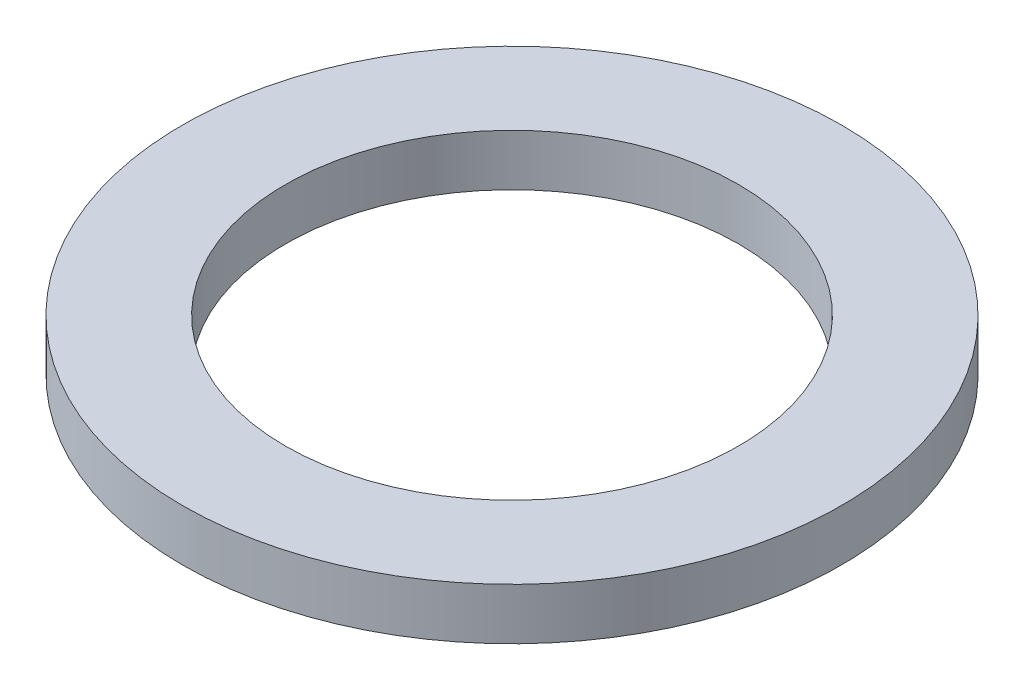
SolidWorks part; units mm, degrees
ref_plane "Plan de face" through (0, 0, 0) normal (0, 0, 1) x (1, 0, 0)
ref_plane "Plan de dessus" through (0, 0, 0) normal (0, 1, 0) x (1, 0, 0)
ref_plane "Plan de droite" through (0, 0, 0) normal (1, 0, 0) x (0, 0, -1)
sketch "Esquisse1" plane through (0, 0, 0) normal (0, 1, 0) x (1, 0, 0)
  circle A0 centre (0, 0) radius 1.6
  circle A1 centre (0, 0) radius 1.1
  dimension "D1" = 3.2
  dimension "D2" = 2.2
extrude "Boss.-Extru.1" add sketch "Esquisse1" along normal blind 0.25
